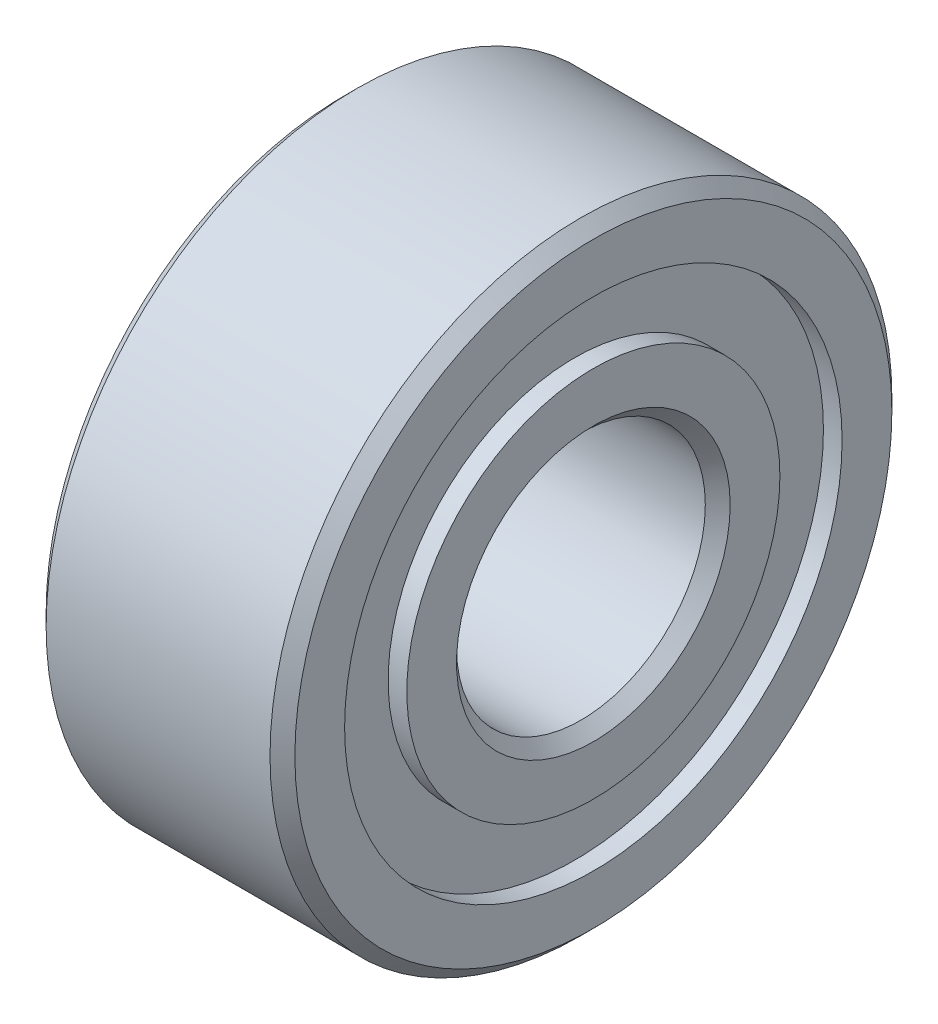
SolidWorks part; units mm, degrees
ref_plane "前视基准面" through (0, 0, 0) normal (0, 0, 1) x (1, 0, 0)
ref_plane "上视基准面" through (0, 0, 0) normal (0, 1, 0) x (1, 0, 0)
ref_plane "右视基准面" through (0, 0, 0) normal (1, 0, 0) x (0, 0, -1)
sketch "草图1" plane through (0, 0, 0) normal (1, 0, 0) x (0, 0, -1)
  circle A0 centre (0, 0) radius 2
  circle A1 centre (0, 0) radius 5
  dimension "D1" = 4
  dimension "D2" = 10
extrude "凸台-拉伸1" add sketch "草图1" along normal blind 4
sketch "草图2" plane through (4, 0, 0) normal (1, 0, 0) x (0, 0, -1)
  circle A0 centre (-0.0004, 0) radius 4
  circle A1 centre (-0.0004, 0) radius 3
  dimension "D1" = 6
  dimension "D2" = 8
extrude "切除-拉伸1" cut sketch "草图2" against normal blind 0.3
chamfer "倒角1" distance 0.2 angle 45 4 edges at (4, 0, -5) (0, 0, -5) (4, 0, -2) (0, 0, -2)
sketch "草图3" plane through (0, 0, 0) normal (-1, 0, 0) x (0, 0, 1)
  circle A0 centre (0, 0) radius 3
  circle A1 centre (0, 0) radius 4
  dimension "D1" = 6
  dimension "D2" = 8
extrude "切除-拉伸2" cut sketch "草图3" against normal blind 0.3
